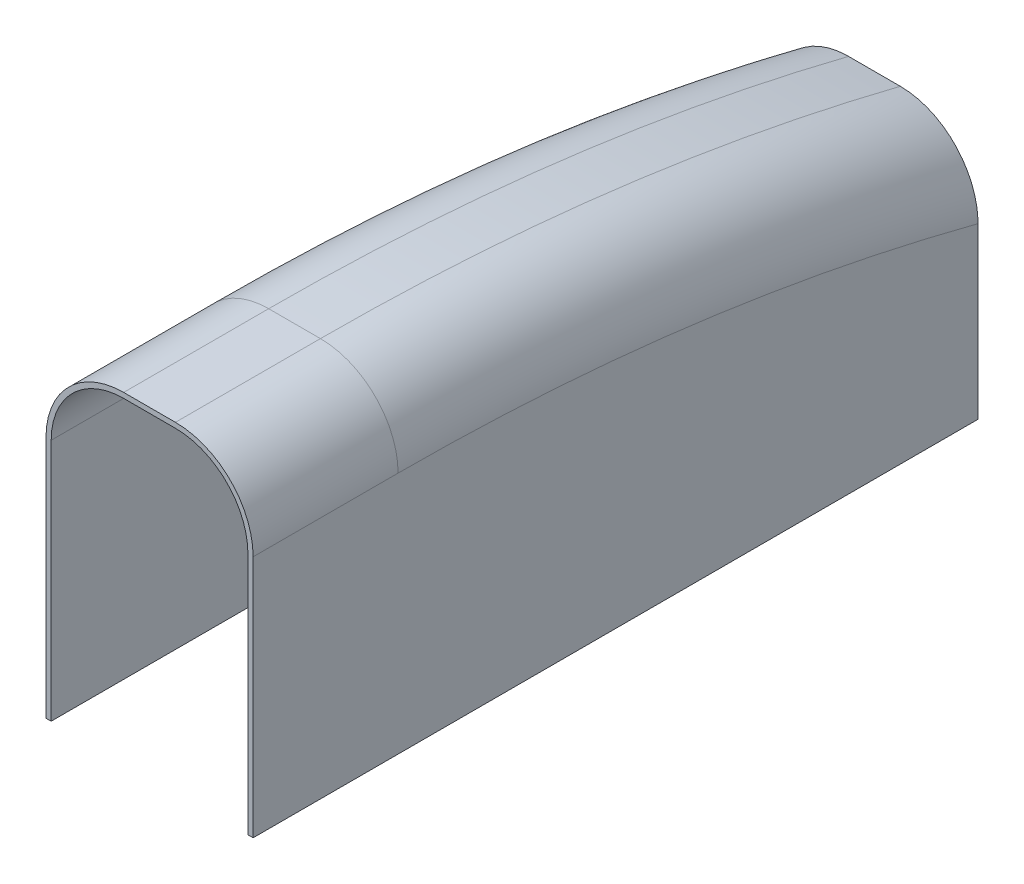
SolidWorks part; units mm, degrees
ref_plane "Front Plane" through (0, 0, 0) normal (0, 0, 1) x (1, 0, 0)
ref_plane "Top Plane" through (0, 0, 0) normal (0, 1, 0) x (1, 0, 0)
ref_plane "Right Plane" through (0, 0, 0) normal (1, 0, 0) x (0, 0, -1)
sketch "Sketch2" plane through (0, 0, 0) normal (0, 0, 1) x (1, 0, 0)
  line L1 (-25.4, -39.37) -> (25.4, -39.37)
  line L2 (-25.4, -39.37) -> (-25.4, 39.37)
  line L3 (-25.4, 39.37) -> (25.4, 39.37)
  line L4 (25.4, -39.37) -> (25.4, 39.37)
  line L5 (-25.4, -39.37) -> (25.4, 39.37) construction
  line L6 (-25.4, 39.37) -> (25.4, -39.37) construction
  point P0 (0, 0)
  dimension "D1" = 78.74
  dimension "D2" = 50.8
sketch "Sketch3" plane through (0, 0, 0) normal (1, 0, 0) x (0, 0, -1)
  line L0 (0, 39.37) -> (35.56, 39.37)
  line L1 (0, 39.37) -> (0, -39.37) construction
  line L2 (0, -39.37) -> (0, 39.37) construction
  line L4 (0, -39.37) -> (177.8, -39.37)
  line L5 (0, -39.37) -> (0, 39.37) construction
  line L6 (0, -39.37) -> (0, 39.37) construction
  line L7 (177.8, -39.37) -> (177.8, 21.844)
  line L8 (0, 39.37) -> (0, -39.37)
  arc A0 (35.56, 39.37) -> (177.8, 21.844) centre (35.56, -546.5988) cw
  dimension "D1" = 35.56
  dimension "D4" = 177.8
  dimension "D2" = 17.526
extrude "Boss-Extrude1" add sketch "Sketch3" along normal up to vertex (25.4 mm away) and the other way up to vertex (25.4 mm away) up to point (25.4, 39.37, 0) other way up to point (-25.4, 39.37, 0)
fillet "Fillet1" radius 19.05 4 edges at (25.4, 39.37, -17.78) (-25.4, 39.37, -17.78) (25.4, 34.972, -107.2178) (-25.4, 34.972, -107.2178)
shell "Shell1" thickness 1.27
sketch "Sketch4" plane through (0, 0, -177.8) normal (0, 0, -1) x (-1, 0, 0)
  line L0 (-6.35, 21.844) -> (6.35, 21.844) construction
  line L1 (25.4, 39.37) -> (-25.4, 39.37) construction
  circle A0 centre (0, -11.5775) radius 5.5626
  point P5 (0, 21.844)
  dimension "D1" = 50.9475
  dimension "D2" = 11.1252
extrude "Cut-Extrude1" cut sketch "Sketch4" against normal blind 50.9475
